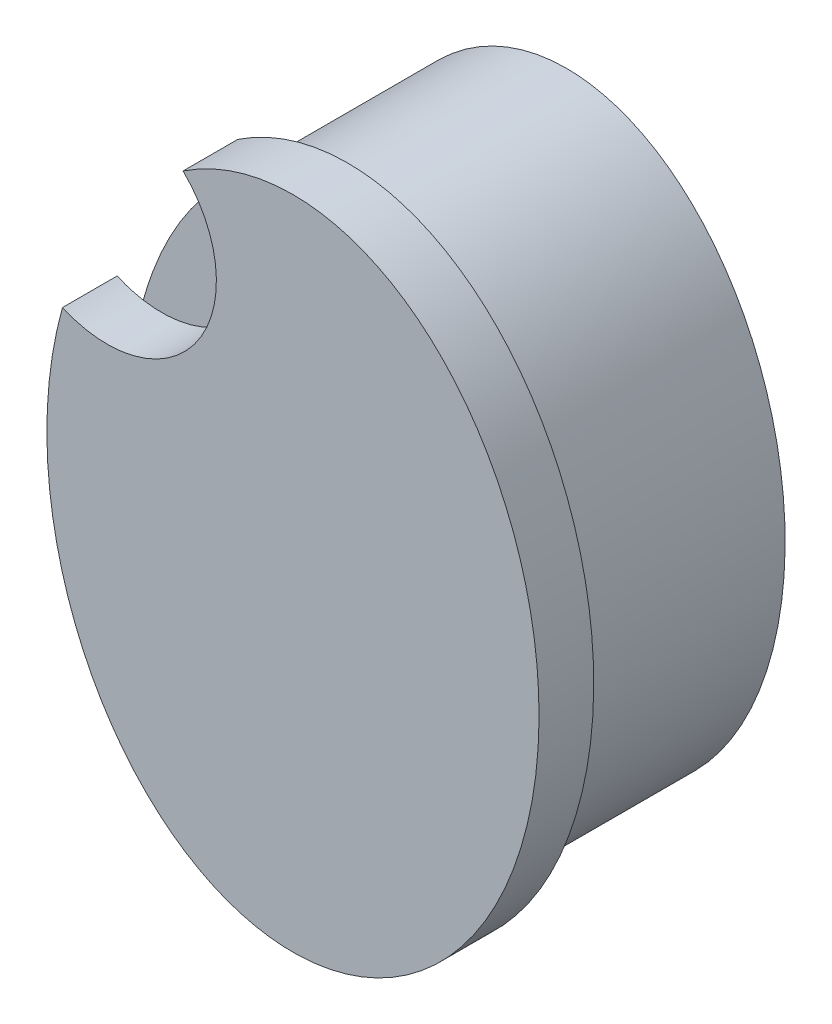
SolidWorks part; units mm, degrees
ref_plane "Alzado" through (0, 0, 0) normal (0, 0, 1) x (1, 0, 0)
ref_plane "Planta" through (0, 0, 0) normal (0, 1, 0) x (1, 0, 0)
ref_plane "Vista lateral" through (0, 0, 0) normal (1, 0, 0) x (0, 0, -1)
sketch "Croquis1" plane through (0, 0, 0) normal (0, 0, 1) x (1, 0, 0)
  ellipse E0 centre (0, 0) end of major axis (0, 11) minor radius 8
extrude "Saliente-Extruir1" add sketch "Croquis1" along normal blind 8
sketch "Croquis2" plane through (0, 0, 8) normal (0, 0, 1) x (1, 0, 0)
  ellipse E0 centre (0, 0) end of major axis (0, 12) minor radius 9
extrude "Saliente-Extruir2" add sketch "Croquis2" along normal blind 2
sketch "Croquis3" plane through (0, 0, 10) normal (0, 0, 1) x (1, 0, 0)
  line L0 (0, 0) -> (0, 3.9368)
  line L1 (0, 3.9368) -> (-4, 3.9368)
  line L2 (0, 3.9368) -> (4, 3.9368)
  circle A0 centre (-6.8003, 7.8606) radius 4
  ellipse E0 centre (-4, 3.9368) end of major axis (-6.2516, 7.2429) minor radius 2
  ellipse E1 centre (4, 3.9368) end of major axis (6.2681, 7.2316) minor radius 2
  ellipse E2 centre (0, 0) end of major axis (0, 12) minor radius 9 construction
  ellipse M3 centre (0, 0) end of major axis (0, 12) minor radius 9
extrude "Cortar-Extruir1" cut sketch "Croquis3" against normal blind 2 contours A0 E0 | E0 A0 M3
